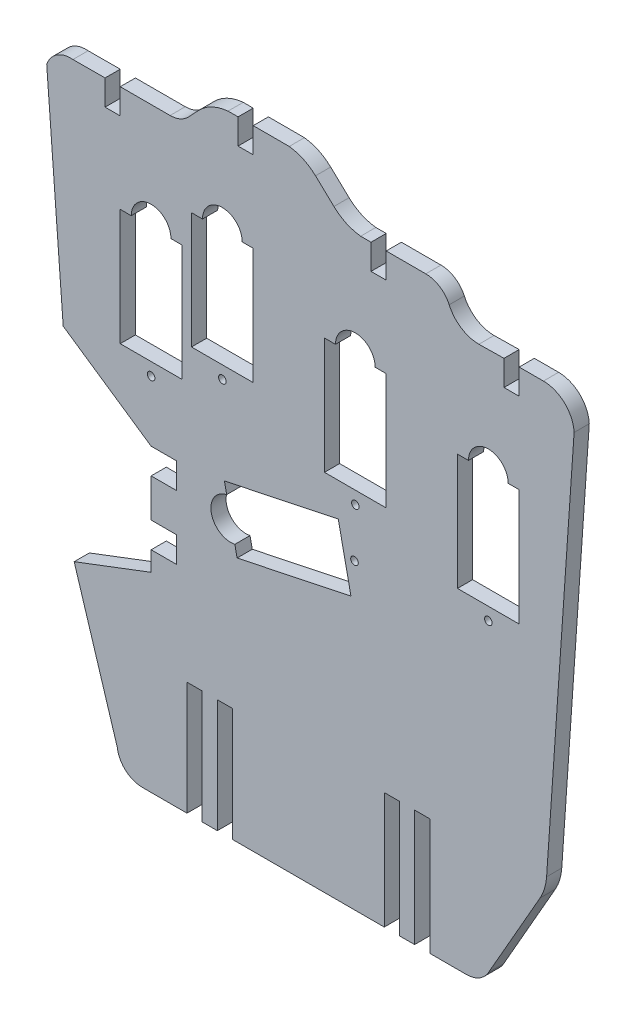
SolidWorks part; units mm, degrees
material "Acrylic (Medium-high impact)"
ref_plane "Front Plane" through (0, 0, 0) normal (0, 0, 1) x (1, 0, 0)
ref_plane "Top Plane" through (0, 0, 0) normal (0, 1, 0) x (1, 0, 0)
ref_plane "Right Plane" through (0, 0, 0) normal (1, 0, 0) x (0, 0, -1)
sketch "Sketch1" plane through (0, 0, 0) normal (0, 0, 1) x (1, 0, 0)
  line L3 (22.6007, 98.0558) -> (24.5521, 100.1239)
  line L5 (47.7146, 100.5321) -> (51.3512, 97.1007)
  line L51 (87.9781, 87.9218) -> (87.9781, 82.9218)
  line L52 (87.9781, 82.9218) -> (84.9781, 82.9218)
  line L53 (84.9781, 82.9218) -> (84.9781, 87.9218)
  line L54 (58.6881, 94.6538) -> (58.6881, 89.6538)
  line L57 (61.6881, 94.6538) -> (61.6881, 89.6538)
  line L58 (61.6881, 89.6538) -> (58.6881, 89.6538)
  line L72 (9.1081, 96.4872) -> (9.1081, 91.4872)
  line L74 (6.1081, 91.4872) -> (6.1081, 96.4872)
  line L78 (9.1081, 91.4872) -> (6.1081, 91.4872)
  line L98 (87.9781, 66.9218) -> (75.7781, 66.9218)
  line L99 (87.9781, 66.9218) -> (87.9781, 43.9218)
  line L100 (87.9781, 43.9218) -> (75.7781, 43.9218)
  line L101 (75.7781, 66.9218) -> (75.7781, 43.9218)
  line L102 (61.6881, 73.6538) -> (49.4881, 73.6538)
  line L103 (61.6881, 73.6538) -> (61.6881, 50.6538)
  line L104 (61.6881, 50.6538) -> (49.4881, 50.6538)
  line L105 (49.4881, 73.6538) -> (49.4881, 50.6538)
  line L106 (35.3981, 81.9679) -> (23.1981, 81.9679)
  line L107 (35.3981, 81.9679) -> (35.3981, 58.9679)
  line L108 (35.3981, 58.9679) -> (23.1981, 58.9679)
  line L109 (23.1981, 81.9679) -> (23.1981, 58.9679)
  line L110 (21.3081, 75.4872) -> (9.1081, 75.4872)
  line L111 (21.3081, 75.4872) -> (21.3081, 52.4872)
  line L112 (21.3081, 52.4872) -> (9.1081, 52.4872)
  line L113 (9.1081, 75.4872) -> (9.1081, 52.4872)
  line L119 (98.839, 82.1578) -> (93.3994, 3.3544)
  line L120 (-5.4259, 93.0205) -> (-2.166, 49.8405)
  line L123 (15.2195, 37.9894) -> (20.2195, 37.9894)
  line L124 (67.3048, -21.2972) -> (64.3048, -21.2972)
  line L131 (15.2195, 32.9094) -> (20.2195, 32.9094)
  line L132 (20.2195, 37.9894) -> (20.2195, 32.9094)
  line L133 (15.2195, 25.3412) -> (20.2195, 25.3412)
  line L135 (15.2195, 20.2612) -> (20.2195, 20.2612)
  line L136 (20.2195, 25.3412) -> (20.2195, 20.2612)
  line L138 (15.2195, 32.9094) -> (15.2195, 25.3412)
  line L139 (15.2195, 20.2612) -> (15.2195, 16.3994)
  line L141 (77.5627, -21.2972) -> (70.3048, -21.2972)
  line L143 (61.3048, -21.2972) -> (31.3048, -21.2972)
  line L145 (70.3048, -21.2972) -> (70.3048, 1.7416)
  line L146 (70.3048, 1.7416) -> (67.3048, 1.7416)
  line L147 (67.3048, -21.2972) -> (67.3048, 1.7416)
  line L149 (64.3048, -21.2972) -> (64.3048, 1.7416)
  line L150 (64.3048, 1.7416) -> (61.3048, 1.7416)
  line L151 (61.3048, -21.2972) -> (61.3048, 1.7416)
  line L153 (31.3048, -21.2972) -> (31.3048, 1.1309)
  line L154 (31.3048, 1.1309) -> (28.3048, 1.1309)
  line L155 (28.3048, -21.2972) -> (28.3048, 1.1309)
  line L157 (22.3048, -21.2972) -> (22.3048, 1.1309)
  line L158 (22.3048, 1.1309) -> (25.3048, 1.1309)
  line L159 (25.3048, -21.2972) -> (25.3048, 1.1309)
  line L160 (28.3048, -21.2972) -> (25.3048, -21.2972)
  line L172 (15.2195, 37.9894) -> (-2.166, 49.8405)
  line L175 (92.1064, -0.917) -> (81.9043, -18.7772)
  line L179 (15.2195, 16.3994) -> (0, 10.6096)
  line L181 (13.483, -21.2972) -> (22.3048, -21.2972)
  line L184 (0, 10.6096) -> (15.2195, 16.3994) construction
  line L185 (0, 10.6096) -> (8.517, -16.8789)
  line L186 (9.1081, 91.4872) -> (9.1081, 75.4872) construction
  line L195 (35.3981, 97.9679) -> (35.3981, 81.9679) construction
  line L197 (32.3981, 102.9679) -> (32.3981, 97.9679)
  line L198 (32.3981, 97.9679) -> (35.3981, 97.9679)
  line L199 (35.3981, 97.9679) -> (35.3981, 102.9679)
  line L202 (61.6881, 89.6538) -> (61.6881, 73.6538) construction
  line L203 (9.1081, 83.4872) -> (35.3981, 83.4872) construction
  line L204 (35.3981, 83.4872) -> (61.6881, 83.4872) construction
  line L205 (87.9781, 82.9218) -> (87.9781, 66.9218) construction
  line L206 (61.6881, 73.6538) -> (87.9781, 73.6538) construction
  line L207 (9.1081, 96.4872) -> (18.964, 96.4872)
  line L208 (30.4232, 102.9679) -> (32.3981, 102.9679)
  line L209 (35.3981, 102.9679) -> (42.522, 102.9679)
  line L210 (56.6388, 94.6538) -> (58.6881, 94.6538)
  line L211 (87.9781, 87.9218) -> (92.7707, 87.9218)
  line L212 (61.6881, 94.6538) -> (69.5167, 94.6538)
  line L213 (80.0083, 87.8422) -> (84.9781, 87.9218)
  line L214 (-0.2418, 96.4691) -> (6.1081, 96.4872)
  arc A5 (51.3512, 97.1007) -> (56.6388, 94.6538) centre (57.6504, 103.7764) ccw
  arc A6 (42.522, 102.9679) -> (47.7146, 100.5321) centre (41.4155, 93.8563) cw
  arc A7 (24.5521, 100.1239) -> (30.4232, 102.9679) centre (31.2278, 93.8247) cw
  arc A12 (-0.2418, 96.4691) -> (-5.4259, 93.0205) centre (-0.6668, 91.4872) ccw
  arc A21 (81.9043, -18.7772) -> (77.5627, -21.2972) centre (77.5627, -16.2972) cw
  arc A23 (93.3994, 3.3544) -> (92.1064, -0.917) centre (83.4232, 4.0431) cw
  arc A24 (8.517, -16.8789) -> (13.483, -21.2972) centre (13.483, -16.2972) ccw
  arc A25 (69.5167, 94.6538) -> (74.1403, 91.6622) centre (69.5167, 89.585) cw
  arc A26 (74.1403, 91.6622) -> (80.0083, 87.8422) centre (80.0444, 94.3146) ccw
  arc A27 (92.7707, 87.9218) -> (98.839, 82.1578) centre (92.7707, 81.8455) cw
  arc A28 (22.6007, 98.0558) -> (18.964, 96.4872) centre (18.964, 101.4872) cw
  point P12 (-9.2732, 96.4872)
  point P18 (80.0035, 87.8515)
  point P88 (80.4648, -21.2972)
  point P90 (80.4648, -21.2972)
  point P93 (12.284, -21.2972)
  point P96 (93.2418, 1.0707)
  point P99 (12.284, -21.2972)
  point P104 (21.1206, 96.4872)
  dimension "D2" = 81.28
  dimension "D6" = 5
  dimension "D11" = 5
  dimension "D12" = 12.2
  dimension "D5" = 5
  dimension "D7" = 5
  dimension "D22" = 3
  dimension "D8" = 5
  dimension "D26" = 10
  dimension "D28" = 5
  dimension "D4" = 43.18
  dimension "D9" = 16
  dimension "D10" = 6.35
  dimension "D13" = 5
  dimension "D14" = 3
  dimension "D15" = 26.29
  dimension "D16" = 23
  dimension "D17" = 5
  dimension "D18" = 5
  dimension "D19" = 5.08
  dimension "D20" = 5.08
  dimension "D21" = 10.0209
  dimension "D23" = 3
  dimension "D24" = 3
  dimension "D25" = 10.16
  dimension "D27" = 5
  dimension "D29" = 30
  dimension "D30" = 16
  dimension "D31" = 26.29
  dimension "D32" = 26.29
  dimension "D33" = 3
extrude "Boss-Extrude1" add sketch "Sketch1" along normal blind 3
sketch "Sketch4" plane through (0, 0, 0) normal (0, 0, -1) x (-1, 0, 0)
  line L0 (-52.2082, 44.0223) -> (-29.7015, 39.2841)
  line L1 (-52.2082, 44.0223) -> (-54.7215, 32.084)
  line L2 (-54.7215, 32.084) -> (-32.2149, 27.3458)
  line L3 (-29.7015, 39.2841) -> (-32.2149, 27.3458)
  dimension "D1" = 23
  dimension "D2" = 12.2
extrude "Cut-Extrude2" cut sketch "Sketch4" against normal through all contours L3 L2 L1 L0
sketch "Sketch5" plane through (0, 0, 3) normal (0, 0, 1) x (1, 0, 0)
  line L0 (21.3081, 75.4872) -> (9.1081, 75.4872) construction
  line L1 (35.3981, 81.9679) -> (23.1981, 81.9679) construction
  line L2 (61.6881, 73.6538) -> (49.4881, 73.6538) construction
  line L3 (87.9781, 66.9218) -> (75.7781, 66.9218) construction
  circle A0 centre (15.2081, 75.4872) radius 3.925
  circle A1 centre (29.2981, 81.9679) radius 3.925
  circle A2 centre (55.5881, 73.6538) radius 3.925
  circle A3 centre (81.8781, 66.9218) radius 3.925
  dimension "D1" = 7.85
extrude "Cut-Extrude3" cut sketch "Sketch5" against normal through all
sketch "Sketch6" plane through (0, 0, 3) normal (0, 0, 1) x (1, 0, 0)
  line L0 (15.2081, 52.4872) -> (15.2081, 49.9872) construction
  line L1 (9.1081, 52.4872) -> (21.3081, 52.4872) construction
  line L2 (29.2981, 58.9679) -> (29.2981, 56.4679) construction
  line L3 (23.1981, 58.9679) -> (35.3981, 58.9679) construction
  line L4 (55.5881, 50.6538) -> (55.5881, 48.1538) construction
  line L5 (49.4881, 50.6538) -> (61.6881, 50.6538) construction
  line L6 (81.8781, 43.9218) -> (81.8781, 41.4218) construction
  line L7 (75.7781, 43.9218) -> (87.9781, 43.9218) construction
  circle A0 centre (15.2081, 49.9872) radius 0.75
  circle A1 centre (29.2981, 56.4679) radius 0.75
  circle A2 centre (55.5881, 48.1538) radius 0.75
  circle A3 centre (81.8781, 41.4218) radius 0.75
  dimension "D1" = 1.5
  dimension "D2" = 2.5
extrude "Cut-Extrude4" cut sketch "Sketch6" against normal through all
sketch "Sketch7" plane through (0, 0, 0) normal (0, 0, -1) x (-1, 0, 0)
  line L1 (-29.7015, 39.2841) -> (-32.2149, 27.3458) construction
  line L2 (-53.4648, 38.0532) -> (-52.76, 36.1815) construction
  line L4 (-52.2082, 44.0223) -> (-54.7215, 32.084) construction
  circle A2 centre (-30.9582, 33.3149) radius 3.93
  circle A4 centre (-52.76, 36.1815) radius 0.75
  point P1 (-52.76, 36.1815)
  dimension "D1" = 7.86
  dimension "D3" = 1.5
  dimension "D2" = 2
extrude "Cut-Extrude5" cut sketch "Sketch7" against normal through all
sketch "Sketch8" plane through (0, 0, 3) normal (0, 0, 1) x (1, 0, 0)
  line L0 (53.4648, 38.0532) -> (55.4219, 38.4652) construction
  line L1 (54.7215, 32.084) -> (52.2082, 44.0223) construction
  circle A0 centre (55.4219, 38.4652) radius 0.75
  dimension "D2" = 1.5
  dimension "D1" = 2
extrude "Cut-Extrude6" cut sketch "Sketch8" against normal through all
